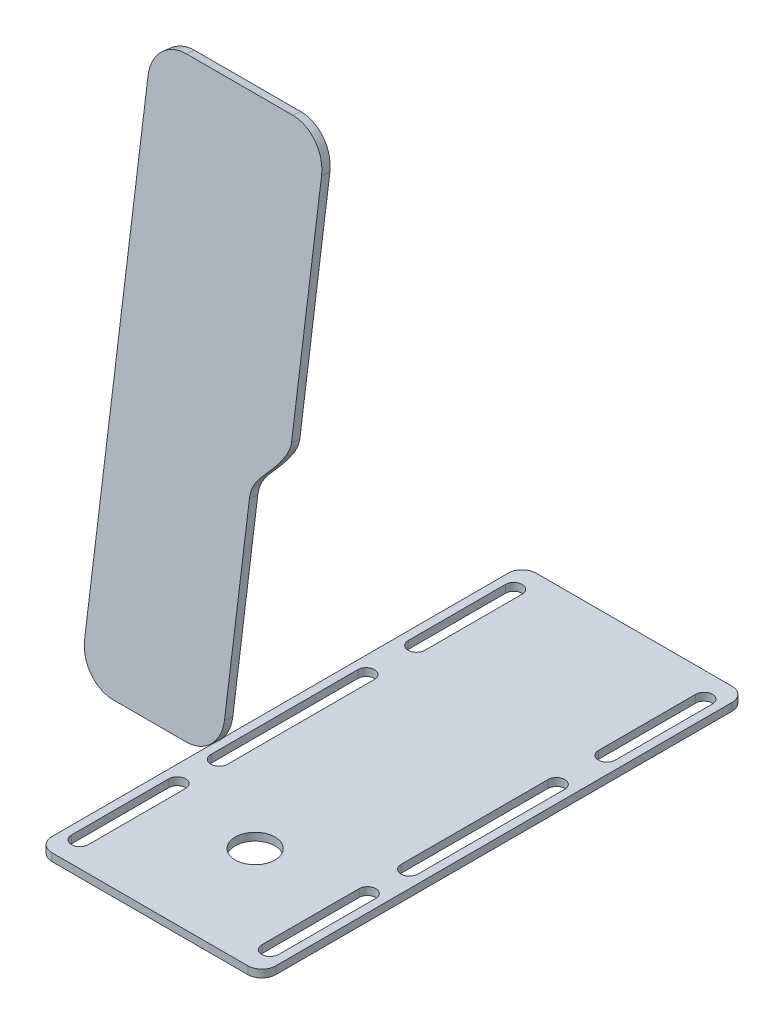
SolidWorks part; units mm, degrees
ref_plane "Front Plane" through (0, 0, 0) normal (0, 0, 1) x (1, 0, 0)
ref_plane "Top Plane" through (0, 0, 0) normal (0, 1, 0) x (1, 0, 0)
ref_plane "Right Plane" through (0, 0, 0) normal (1, 0, 0) x (0, 0, -1)
sketch "Sketch1" plane through (0, 0, 0) normal (0, 1, 0) x (1, 0, 0)
  line L0 (34, 77.5187) -> (34, 42.7687) construction
  line L1 (-35, 86.5188) -> (35, 86.5188)
  line L2 (-40, 81.5187) -> (-40, -81.5187)
  line L3 (-35, -86.5187) -> (35, -86.5187)
  line L4 (40, 81.5187) -> (40, -81.5187)
  line L5 (-40, 86.5188) -> (40, -86.5187) construction
  line L6 (-40, -86.5187) -> (40, 86.5188) construction
  line L7 (37, 77.5187) -> (37, 42.7687)
  line L8 (31, 77.5187) -> (31, 42.7687)
  line L9 (-40, 0) -> (40, 0) construction
  line L10 (0, 86.5188) -> (0, -86.5187) construction
  line L11 (-34, 77.5187) -> (-34, 42.7687) construction
  line L12 (-37, 77.5187) -> (-37, 42.7687)
  line L13 (-31, 77.5187) -> (-31, 42.7687)
  line L14 (34, -77.5187) -> (34, -42.7687) construction
  line L15 (37, -77.5187) -> (37, -42.7687)
  line L16 (31, -77.5187) -> (31, -42.7687)
  line L17 (-34, -77.5187) -> (-34, -42.7687) construction
  line L18 (-37, -77.5187) -> (-37, -42.7687)
  line L19 (-31, -77.5187) -> (-31, -42.7687)
  line L20 (34, 24.7687) -> (34, -27.7687) construction
  line L21 (37, 24.7687) -> (37, -27.7687)
  line L22 (31, 24.7687) -> (31, -27.7687)
  line L23 (-34, 24.7687) -> (-34, -27.7687) construction
  line L24 (-37, 24.7687) -> (-37, -27.7687)
  line L25 (-31, 24.7687) -> (-31, -27.7687)
  arc A0 (-40, -81.5187) -> (-35, -86.5187) centre (-35, -81.5187) ccw
  arc A1 (35, -86.5187) -> (40, -81.5187) centre (35, -81.5187) ccw
  arc A2 (35, 86.5188) -> (40, 81.5187) centre (35, 81.5187) cw
  arc A3 (-35, 86.5188) -> (-40, 81.5187) centre (-35, 81.5187) ccw
  arc A4 (37, 77.5187) -> (31, 77.5187) centre (34, 77.5187) ccw
  arc A5 (31, 42.7687) -> (37, 42.7687) centre (34, 42.7687) ccw
  arc A6 (-37, 77.5187) -> (-31, 77.5187) centre (-34, 77.5187) cw
  arc A7 (-31, 42.7687) -> (-37, 42.7687) centre (-34, 42.7687) cw
  arc A8 (37, -77.5187) -> (31, -77.5187) centre (34, -77.5187) cw
  arc A9 (31, -42.7687) -> (37, -42.7687) centre (34, -42.7687) cw
  arc A10 (-37, -77.5187) -> (-31, -77.5187) centre (-34, -77.5187) ccw
  arc A11 (-31, -42.7687) -> (-37, -42.7687) centre (-34, -42.7687) ccw
  arc A12 (37, 24.7687) -> (31, 24.7687) centre (34, 24.7687) ccw
  arc A13 (31, -27.7687) -> (37, -27.7687) centre (34, -27.7687) ccw
  arc A14 (-37, 24.7687) -> (-31, 24.7687) centre (-34, 24.7687) cw
  arc A15 (-31, -27.7687) -> (-37, -27.7687) centre (-34, -27.7687) cw
  circle A16 centre (0, -48.9201) radius 7.112
  point P0 (0, 0)
  point P20 (34, 60.1437)
  point P31 (-34, 60.1437)
  point P38 (34, -60.1437)
  point P45 (-34, -60.1437)
  point P52 (34, -1.5)
  point P59 (-34, -1.5)
  dimension "D3" = 5
  dimension "D6" = 6
  dimension "D5" = 40.75
  dimension "D9" = 12
  dimension "D10" = 9
  dimension "D1" = 80
  dimension "D2" = 173.0375
  dimension "D4" = 3
  dimension "D7" = 6
  dimension "D8" = 6
extrude "Boss-Extrude1" add sketch "Sketch1" along normal blind 2.75
sketch "Sketch2" plane through (0, 0, 0) normal (1, 0, 0) x (0, 0, -1)
  line L0 (-60.5187, 248) -> (-86.5187, 61)
  line L1 (-86.5187, 89.4829) -> (-86.5187, 186.7974) construction
  line L2 (-81.5187, 0) -> (81.5187, 0) construction
  point P7 (0, 0)
  dimension "D1" = 188.7988
  dimension "D2" = 26
  dimension "D3" = 61
  dimension "D4" = 248
  dimension "D5" = 82.084
ref_plane "Plane1" through (0, 12.9581, 93.1984) normal (0, 0.1377, 0.9905) x (0, -0.9905, 0.1377)
sketch "Sketch3" plane through (0, 12.9581, 93.1984) normal (0, 0.1377, 0.9905) x (0, -0.9905, 0.1377)
  line L0 (-237.3029, 0) -> (-48.5041, 0) construction
  line L1 (-125.3029, 25) -> (-60.5041, 25)
  line L2 (-237.3029, 25) -> (-237.3029, -13)
  line L3 (-225.3029, -25) -> (-60.5041, -25)
  line L4 (-48.5041, 13) -> (-48.5041, -13)
  line L5 (-237.3029, 0) -> (-48.5041, 0) construction
  line L6 (-225.3029, 37) -> (-147.3029, 37)
  line L7 (-147.3029, 37) -> (-125.3029, 25) construction
  arc A1 (-237.3029, -13) -> (-225.3029, -25) centre (-225.3029, -13) ccw
  arc A2 (-60.5041, -25) -> (-48.5041, -13) centre (-60.5041, -13) ccw
  arc A3 (-60.5041, 25) -> (-48.5041, 13) centre (-60.5041, 13) cw
  arc A4 (-225.3029, 37) -> (-237.3029, 25) centre (-225.3029, 25) ccw
  spline S0 degree 3 poles (-147.3029, 37) (-144.0655, 37) (-135.5828, 31) (-129.9806, 25) (-125.3029, 25) knots 0 0 0 0 0.5 1 1 1 1
  point P6 (-124.9036, 32.089)
  point P7 (-48.5041, 0)
  point P18 (-136.3029, 31)
  dimension "D2" = 12
  dimension "D1" = 50
  dimension "D3" = 62
  dimension "D4" = 90
  dimension "D5" = 22
extrude "Boss-Extrude2" add sketch "Sketch3" against normal blind 3 separate body
